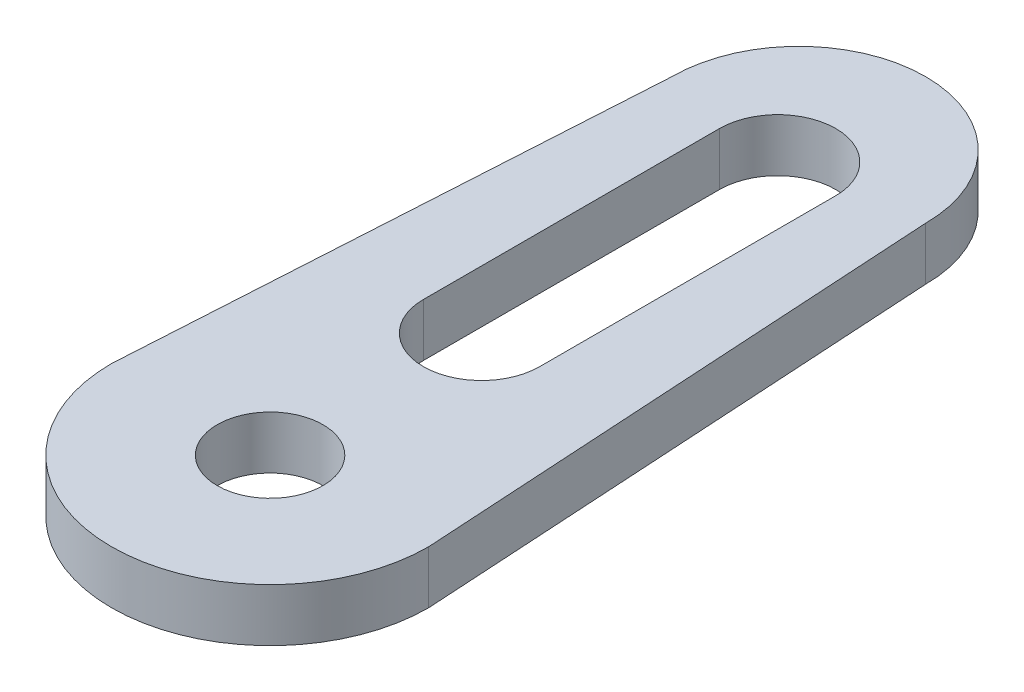
SolidWorks part; units mm, degrees
ref_plane "Front Plane" through (0, 0, 0) normal (0, 0, 1) x (1, 0, 0)
ref_plane "Top Plane" through (0, 0, 0) normal (0, 1, 0) x (1, 0, 0)
ref_plane "Right Plane" through (0, 0, 0) normal (1, 0, 0) x (0, 0, -1)
sketch "Sketch1" plane through (0, 0, 0) normal (0, 1, 0) x (1, 0, 0)
  line L0 (-6, 25) -> (-7.5, 0)
  line L1 (6, 25) -> (7.5, 0)
  arc A0 (-7.5, 0) -> (7.5, 0) centre (0, 0) ccw
  arc A1 (6, 25) -> (-6, 25) centre (0, 25) ccw
  point P1 (7.4462, 0)
  dimension "D1" = 15
  dimension "D2" = 12
  dimension "D3" = 25
extrude "Boss-Extrude1" add sketch "Sketch1" along normal blind 2.5
sketch "Sketch2" plane through (0, 2.5, 0) normal (0, 1, 0) x (1, 0, 0)
  line L0 (0, 24) -> (0, 10) construction
  line L1 (2.75, 24) -> (2.75, 10)
  line L2 (-2.75, 24) -> (-2.75, 10)
  arc A2 (2.75, 24) -> (-2.75, 24) centre (0, 24) ccw
  arc A3 (-2.75, 10) -> (2.75, 10) centre (0, 10) ccw
  circle A5 centre (0, 0) radius 2.5
  point P2 (0, 17)
  dimension "D1" = 5.5
  dimension "D2" = 10
  dimension "D4" = 5
  dimension "D3" = 14
extrude "Cut-Extrude1" cut sketch "Sketch2" against normal through all
